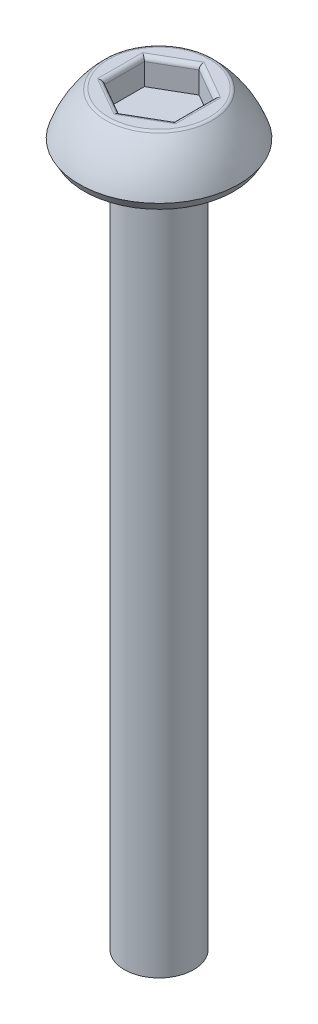
SolidWorks part; units mm, degrees
ref_plane "Front Plane" through (0, 0, 0) normal (0, 0, 1) x (1, 0, 0)
ref_plane "Top Plane" through (0, 0, 0) normal (0, 1, 0) x (1, 0, 0)
ref_plane "Right Plane" through (0, 0, 0) normal (1, 0, 0) x (0, 0, -1)
sketch "Sketch1" plane through (0, 0, 0) normal (1, 0, 0) x (0, 0, -1)
  line L0 (0, 0) -> (0, 1.5) construction
  line L1 (0, 1.5) -> (-1.5, 1.5)
  line L3 (-2.3, 0.25) -> (-2.1557, 0)
  line L4 (-2.1557, 0) -> (-1, 0)
  line L5 (-1, 0) -> (-1, -20)
  line L6 (-1, -20) -> (0, -20)
  line L7 (0, -20) -> (0, 1.5)
  line L8 (0, 0) -> (-1, 0) construction
  arc A0 (-1.5, 1.5) -> (-2.3, 0.25) centre (0.5483, -0.6919) ccw
  dimension "D5" = 3
  dimension "D1" = 1.5
  dimension "D2" = 2.3
  dimension "D3" = 1.5
  dimension "D4" = 0.25
  dimension "D6" = 60
  dimension "D7" = 1
  dimension "D8" = 20
  dimension "D9" = 2.3
revolve "Revolve1" add sketch "Sketch1" angle 360 about L7
sketch "Sketch2" plane through (0, 1.5, 0) normal (0, 1, 0) x (1, 0, 0)
  line L1 (0, 1.1547) -> (-1, 0.5774)
  line L2 (-1, 0.5774) -> (-1, -0.5774)
  line L3 (-1, -0.5774) -> (0, -1.1547)
  line L4 (0, -1.1547) -> (1, -0.5774)
  line L5 (1, -0.5774) -> (1, 0.5774)
  line L6 (1, 0.5774) -> (0, 1.1547)
  circle A0 centre (0, 0) radius 1 construction
  dimension "D1" = 2
extrude "Cut-Extrude1" cut sketch "Sketch2" against normal blind 0.75
fillet "Fillet1" radius 0.125 7 edges at (0, 1.5, -1.5) (-0.5, 1.5, 0.866) (0.5, 1.5, 0.866) (1, 1.5, 0) (0.5, 1.5, -0.866) (-0.5, 1.5, -0.866) (-1, 1.5, 0)
